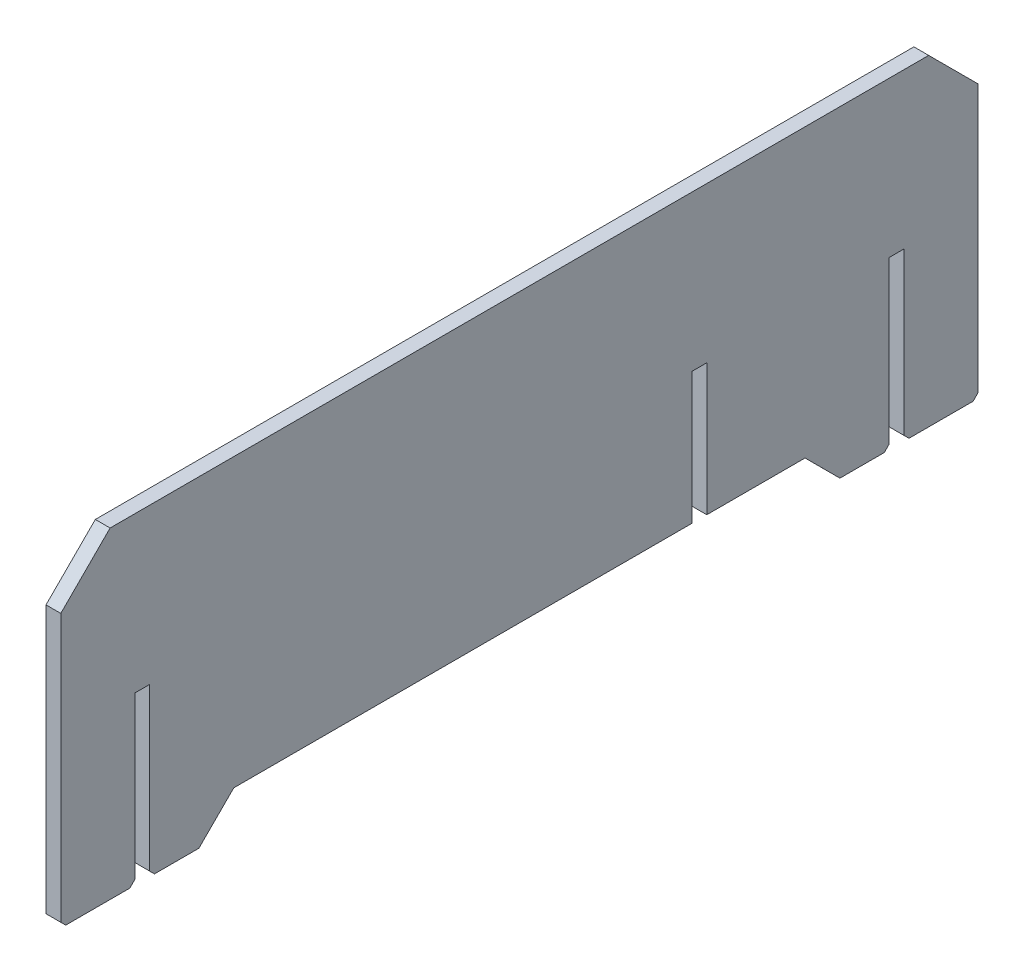
SolidWorks part; units mm, degrees
ref_plane "Front Plane" through (0, 0, 0) normal (0, 0, 1) x (1, 0, 0)
ref_plane "Top Plane" through (0, 0, 0) normal (0, 1, 0) x (1, 0, 0)
ref_plane "Right Plane" through (0, 0, 0) normal (1, 0, 0) x (0, 0, -1)
sketch "Sketch1" plane through (0, 0, 0) normal (0, 0, 1) x (1, 0, 0)
  line L0 (-261.4898, -119.5144) -> (-93.1848, -119.5144) construction
  line L1 (-268.5609, -126.5854) -> (-261.4898, -119.5144) construction
  line L2 (-227.1279, -66.1297) -> (-223.1279, -66.1297) construction
  line L3 (-232.3373, -36.5854) -> (-227.1279, -66.1297) construction
  line L4 (-261.4898, -119.5144) -> (-93.1848, -119.5144)
  line L5 (-268.5609, -126.5854) -> (-261.4898, -119.5144)
  line L6 (-227.1279, -66.1297) -> (-223.1279, -66.1297)
  line L7 (-232.3373, -36.5854) -> (-227.1279, -66.1297)
  line L8 (-227.1279, -66.1297) -> (-222.1279, -66.1297) construction
  line L10 (-222.1279, -61.3381) -> (-219.1279, -61.3381)
  line L11 (-222.1279, -61.3381) -> (-222.1279, -126.5881)
  line L12 (-222.1279, -126.5881) -> (-219.1279, -126.5881)
  line L13 (-219.1279, -61.3381) -> (-219.1279, -126.5881)
  dimension "D1" = 5
  dimension "D2" = 3
extrude "Boss-Extrude1" add sketch "Sketch1" along normal blind 15 and the other way offset from surface (171 mm away) 15 contours L13 L4 L11 L12 | L13 L6 L11 L4 | L13 L10 L11 L6
sketch "Sketch2" plane through (-219.1279, 0, 0) normal (1, 0, 0) x (0, 0, -1)
  line L0 (113, -126.5854) -> (113, -119.5144) construction
  line L1 (113, -119.5144) -> (116, -119.5144) construction
  line L2 (116, -119.5144) -> (116, -126.5854) construction
  line L3 (116, -126.5854) -> (113, -126.5854) construction
  line L4 (153, -126.5854) -> (153, -119.5144) construction
  line L5 (153, -119.5144) -> (156, -119.5144) construction
  line L6 (156, -119.5144) -> (156, -126.5854) construction
  line L7 (156, -126.5854) -> (153, -126.5854) construction
  line L8 (3, -119.5144) -> (3, -126.5854) construction
  line L9 (3, -126.5854) -> (0, -126.5854) construction
  line L10 (0, -126.5854) -> (0, -119.5144) construction
  line L11 (0, -119.5144) -> (3, -119.5144) construction
  line L12 (3, -36.5854) -> (3, -66.1297) construction
  line L13 (3, -66.1297) -> (0, -66.1297) construction
  line L14 (0, -66.1297) -> (0, -36.5854) construction
  line L15 (0, -36.5854) -> (3, -36.5854) construction
  line L16 (113, -126.5854) -> (113, -119.5144)
  line L17 (113, -119.5144) -> (116, -119.5144)
  line L18 (116, -119.5144) -> (116, -126.5854)
  line L19 (116, -126.5854) -> (113, -126.5854)
  line L20 (153, -126.5854) -> (153, -119.5144)
  line L21 (153, -119.5144) -> (156, -119.5144)
  line L22 (156, -119.5144) -> (156, -126.5854)
  line L23 (156, -126.5854) -> (153, -126.5854)
  line L24 (3, -119.5144) -> (3, -126.5854)
  line L25 (3, -126.5854) -> (0, -126.5854)
  line L26 (0, -126.5854) -> (0, -119.5144)
  line L27 (0, -119.5144) -> (3, -119.5144)
  line L28 (3, -36.5854) -> (3, -66.1297)
  line L29 (3, -66.1297) -> (0, -66.1297)
  line L30 (0, -66.1297) -> (0, -36.5854)
  line L31 (0, -36.5854) -> (3, -36.5854)
  line L32 (3, -66.1297) -> (3, -119.5144) construction
  line L33 (0, -92.822) -> (0, -119.5144)
  line L34 (3, -92.822) -> (0, -92.822)
  line L35 (3, -92.822) -> (3, -119.5144)
  line L36 (171, -61.3381) -> (-15, -61.3381) construction
  line L37 (171, -61.3381) -> (-15, -61.3381)
  line L38 (0, -61.3381) -> (3, -61.3381)
  line L39 (3, -92.822) -> (171, -92.822) construction
  line L40 (171, -61.3381) -> (171, -126.5881) construction
  line L41 (113, -119.5144) -> (113, -92.822)
  line L42 (113, -92.822) -> (116, -92.822)
  line L43 (116, -92.822) -> (116, -119.5144)
  line L44 (153, -119.5144) -> (153, -92.822)
  line L45 (153, -92.822) -> (156, -92.822)
  line L46 (156, -92.822) -> (156, -119.5144)
  line L47 (3, -126.5854) -> (13, -126.5881)
  line L48 (171, -126.5881) -> (-15, -126.5881) construction
  line L49 (13, -126.5881) -> (20.0776, -119.5144)
  line L50 (20.0776, -119.5144) -> (135.93, -119.5144)
  line L51 (135.93, -119.5144) -> (143, -126.5881)
  line L52 (3, -126.5854) -> (3, -128.4772)
  line L53 (3, -128.4772) -> (0, -128.4772)
  line L54 (0, -128.4772) -> (0, -126.5854)
  line L55 (156, -126.5854) -> (156, -129.4479)
  line L56 (156, -129.4479) -> (153, -129.4479)
  line L57 (153, -129.4479) -> (153, -126.5854)
  line M4 (-15, -126.5881) -> (171, -126.5881)
  dimension "D1" = 10
  dimension "D2" = 10
extrude "Cut-Extrude1" cut sketch "Sketch2" against normal up to next contours L27 L26 L25 L24 | L35 L34 L33 L27 | L51 L50 L18 L19 L16 L49 M4 | L19 L18 L17 L16 | L43 L42 L41 L17 | L23 L22 L21 L20 | L46 L45 L44 L21
chamfer "Chamfer1" distance 10 angle 45 2 edges at (-220.6279, -61.3381, -171) (-220.6279, -61.3381, 15)
sketch "Sketch5" plane through (0, -126.5854, 0) normal (0, 1, 0) x (1, 0, 0)
  line L4 (-222.1279, 156) -> (-222.1279, 153)
  line L5 (-222.1279, 153) -> (-219.1279, 153)
  line L6 (-219.1279, 153) -> (-219.1279, 156)
  line L7 (-219.1279, 156) -> (-222.1279, 156)
  line L8 (-222.1279, 156) -> (-222.1279, 153)
  line L9 (-222.1279, 153) -> (-219.1279, 153)
  line L10 (-219.1279, 153) -> (-219.1279, 156)
  line L11 (-219.1279, 156) -> (-222.1279, 156)
  dimension "D1" = 0
extrude "Cut-Extrude2" cut sketch "Sketch5" against normal through all
sketch "Sketch6" plane through (0, -126.5854, 0) normal (0, 1, 0) x (1, 0, 0)
  line L4 (-222.1279, 3) -> (-222.1279, 0)
  line L5 (-222.1279, 0) -> (-219.1279, 0)
  line L6 (-219.1279, 0) -> (-219.1279, 3)
  line L7 (-219.1279, 3) -> (-222.1279, 3)
  line L8 (-222.1279, 3) -> (-222.1279, 0)
  line L9 (-222.1279, 0) -> (-219.1279, 0)
  line L10 (-219.1279, 0) -> (-219.1279, 3)
  line L11 (-219.1279, 3) -> (-222.1279, 3)
  dimension "D1" = 0
extrude "Cut-Extrude3" cut sketch "Sketch6" against normal up to next
chamfer "Chamfer2" distance 1 angle 45 6 edges at (-220.6279, -126.5881, -171) (-220.6279, -126.5881, -153) (-220.6279, -126.5881, -156) (-220.6279, -126.5881, -3) (-220.6279, -126.5881, 0) (-220.6279, -126.5881, 15)
